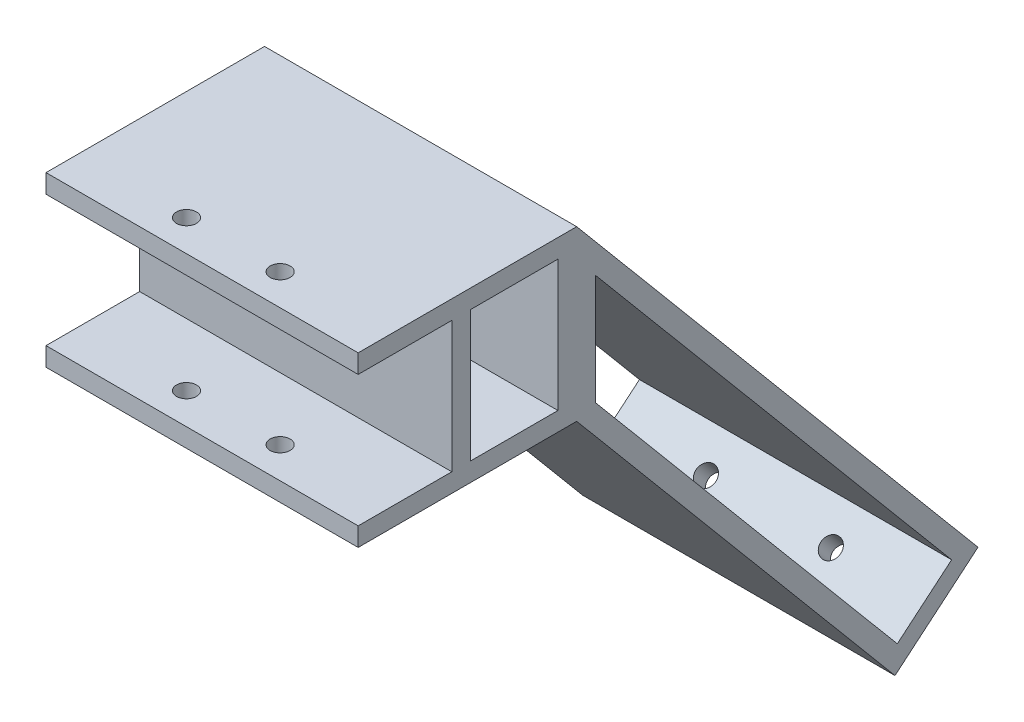
SolidWorks part; units mm, degrees
ref_plane "前视基准面" through (0, 0, 0) normal (0, 0, 1) x (1, 0, 0)
ref_plane "上视基准面" through (0, 0, 0) normal (0, 1, 0) x (1, 0, 0)
ref_plane "右视基准面" through (0, 0, 0) normal (1, 0, 0) x (0, 0, -1)
other "Configuration Table"
sketch "草图1" plane through (0, 0, 0) normal (0, 0, 1) x (1, 0, 0)
  line L1 (-21.1991, 13.3298) -> (28.8009, 13.3298)
  line L2 (-21.1991, 13.3298) -> (-21.1991, -13.6702)
  line L3 (-21.1991, -13.6702) -> (28.8009, -13.6702)
  line L4 (28.8009, 13.3298) -> (28.8009, -13.6702)
  dimension "D1" = 50
  dimension "D2" = 27
extrude "凸台-拉伸1" add sketch "草图1" along normal blind 35
sketch "草图2" plane through (0, 0, 35) normal (0, 0, 1) x (1, 0, 0)
  line L0 (-21.1991, 13.3298) -> (-21.1991, -13.6702) construction
  line L1 (-21.1991, 10.3298) -> (28.8009, 10.3298)
  line L2 (-21.1991, 10.3298) -> (-21.1991, -10.6702)
  line L3 (-21.1991, -10.6702) -> (28.8009, -10.6702)
  line L4 (28.8009, 10.3298) -> (28.8009, -10.6702)
  line L5 (28.8009, -13.6702) -> (28.8009, 13.3298) construction
  line L6 (28.8009, 13.3298) -> (-21.1991, 13.3298) construction
  line L7 (-21.1991, -13.6702) -> (28.8009, -13.6702) construction
  dimension "D1" = 3
  dimension "D2" = 3
extrude "切除-拉伸1" cut sketch "草图2" against normal blind 15
sketch "草图3" plane through (0, -13.6702, 0) normal (0, -1, 0) x (1, 0, 0)
  line L0 (28.8009, 35) -> (28.8009, 0) construction
  line L1 (-21.1991, 35) -> (28.8009, 35)
  line L2 (-21.1991, 35) -> (-21.1991, 25)
  line L3 (-21.1991, 25) -> (28.8009, 25)
  line L4 (28.8009, 35) -> (28.8009, 25)
  line L5 (-21.1991, 30) -> (28.8009, 30) construction
  line L6 (3.8009, 35) -> (3.8009, 25) construction
  circle A0 centre (-3.6991, 30) radius 1.6
  circle A1 centre (11.3009, 30) radius 1.6
  dimension "D4" = 3.2
  dimension "D1" = 10
  dimension "D2" = 7.5
  dimension "D3" = 7.5
extrude "切除-拉伸2" cut sketch "草图3" against normal through all contours A1 | A0
sketch "草图4" plane through (-21.1991, 0, 0) normal (-1, 0, 0) x (0, 0, 1)
  line L0 (35, 13.3298) -> (0, 13.3298) construction
  line L1 (3, 10.3298) -> (17, 10.3298)
  line L2 (3, 10.3298) -> (3, -10.6702)
  line L3 (3, -10.6702) -> (17, -10.6702)
  line L4 (17, 10.3298) -> (17, -10.6702)
  line L5 (35, -13.6702) -> (0, -13.6702) construction
  line L6 (20, 10.3298) -> (20, -10.6702) construction
  line L7 (0, 13.3298) -> (0, -13.6702) construction
  dimension "D1" = 3
  dimension "D2" = 3
  dimension "D3" = 3
  dimension "D4" = 3
extrude "切除-拉伸3" cut sketch "草图4" against normal through all
sketch "草图6" plane through (28.8009, 0, 0) normal (1, 0, 0) x (0, 0, -1)
  line L0 (0, -13.6702) -> (50.9839, -74.4304)
  line L1 (-35, -13.6702) -> (0, -13.6702) construction
  line L2 (50.9839, -74.4304) -> (64.2788, -63.2747)
  line L3 (64.2788, -63.2747) -> (0, 13.3298)
  line L4 (0, 13.3298) -> (0, -13.6702)
  dimension "D1" = 130
  dimension "D2" = 100
extrude "凸台-拉伸2" add sketch "草图6" against normal blind 50
sketch "草图7" plane through (28.8009, 0, 0) normal (1, 0, 0) x (0, 0, -1)
  line L0 (0, 13.3298) -> (0, -13.6702) construction
  line L1 (0, -13.6702) -> (50.9839, -74.4304) construction
  line L2 (50.9839, -74.4304) -> (64.2788, -63.2747) construction
  line L3 (64.2788, -63.2747) -> (0, 13.3298) construction
  line L4 (60.0523, -62.9049) -> (3, 5.0873)
  line L5 (3, 5.0873) -> (3, -12.5783)
  line L6 (3, -12.5783) -> (51.3536, -70.2039)
  line L7 (51.3536, -70.2039) -> (60.0523, -62.9049)
  dimension "D1" = 3
extrude "切除-拉伸4" cut sketch "草图7" against normal through all contours L4 L5 L6 L7
sketch "草图8" plane through (0, -68.7822, -57.7151) normal (0, -0.766, -0.6428) x (-1, 0, 0)
  line L0 (-28.8009, -0.1094) -> (21.1991, -0.1094) construction
  line L1 (-28.8009, -8.7871) -> (-28.8009, 8.5682) construction
  line L2 (21.1991, -8.7871) -> (21.1991, 8.5682) construction
  line L3 (-3.8009, 8.5682) -> (-3.8009, -8.7871) construction
  line L4 (21.1991, 8.5682) -> (-28.8009, 8.5682) construction
  line L5 (21.1991, -8.7871) -> (-28.8009, -8.7871) construction
  circle A0 centre (-13.8009, -0.1094) radius 1.6
  circle A1 centre (6.1991, -0.1094) radius 1.6
  dimension "D1" = 3.2
  dimension "D2" = 10
  dimension "D3" = 10
extrude "切除-拉伸5" cut sketch "草图8" against normal blind 50
